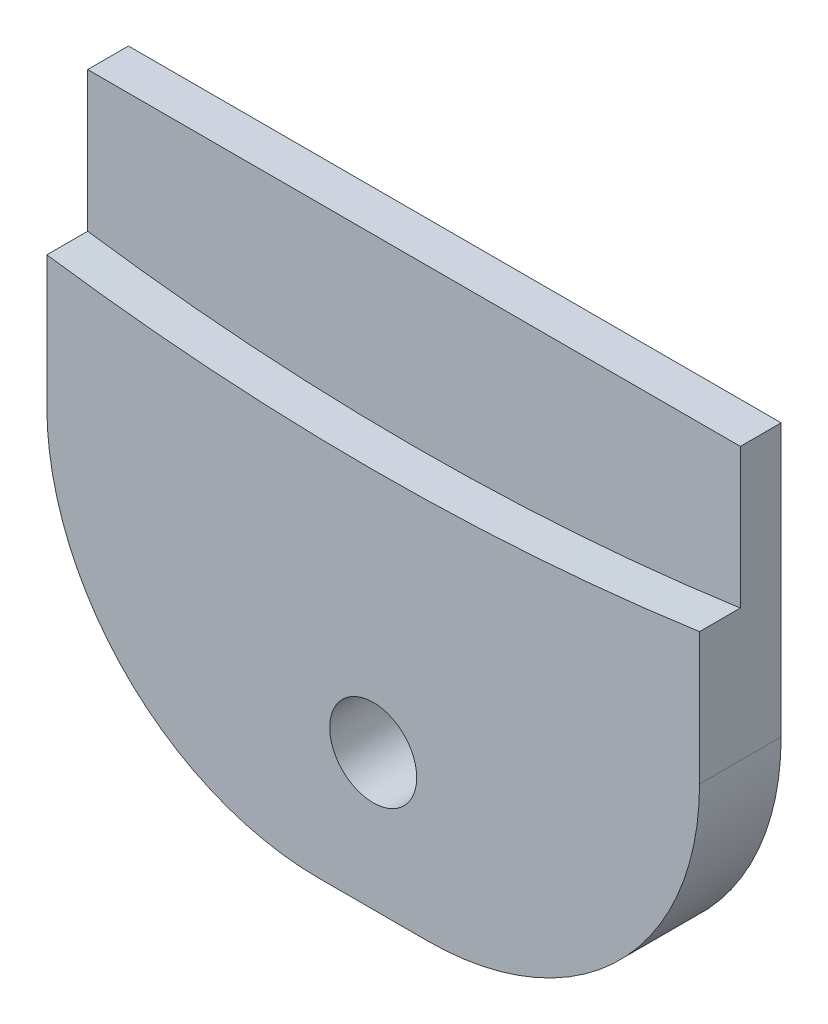
SolidWorks part; units mm, degrees
ref_plane "Front" through (0, 0, 0) normal (0, 0, 1) x (1, 0, 0)
ref_plane "Top" through (0, 0, 0) normal (0, 1, 0) x (1, 0, 0)
ref_plane "Right" through (0, 0, 0) normal (1, 0, 0) x (0, 0, -1)
sketch "Sketch1" plane through (0, 0, 0) normal (0, 0, 1) x (1, 0, 0)
  line L1 (-12, 20) -> (12, 20)
  line L2 (-12, 20) -> (-12, 0)
  line L3 (-12, 0) -> (12, 0)
  line L4 (12, 20) -> (12, 0)
  dimension "D1" = 24
  dimension "D2" = 20
extrude "Boss-Extrude1" add sketch "Sketch1" along normal blind 3
sketch "Sketch3" plane through (0, 0, 3) normal (0, 0, 1) x (1, 0, 0)
  circle A0 centre (0, 5) radius 1.6
  dimension "D1" = 3.2
  dimension "D2" = 5
extrude "Cut-Extrude1" cut sketch "Sketch3" against normal through all
sketch "Sketch2" plane through (0, 0, 3) normal (0, 0, 1) x (1, 0, 0)
  line L0 (12, 0) -> (12, 20) construction
  line L1 (-12, 20) -> (-12, 0) construction
  line L2 (-12, 14) -> (12, 14) construction
  line L3 (-12, 14.8513) -> (-12, 20)
  line L4 (-12, 20) -> (12, 20)
  line L5 (12, 20) -> (12, 14.8513)
  arc A0 (-12, 14.8513) -> (12, 14.8513) centre (0, 99) ccw
  circle A1 centre (0, 5) radius 1.6 construction
  dimension "D1" = 85
  dimension "D2" = 9
extrude "Cut-Extrude2" cut sketch "Sketch2" against normal blind 1.5
fillet "Fillet1" radius 10 2 edges at (-12, 0, 1.5) (12, 0, 1.5)
equation "\"D2@Sketch2\" = 94-85"
